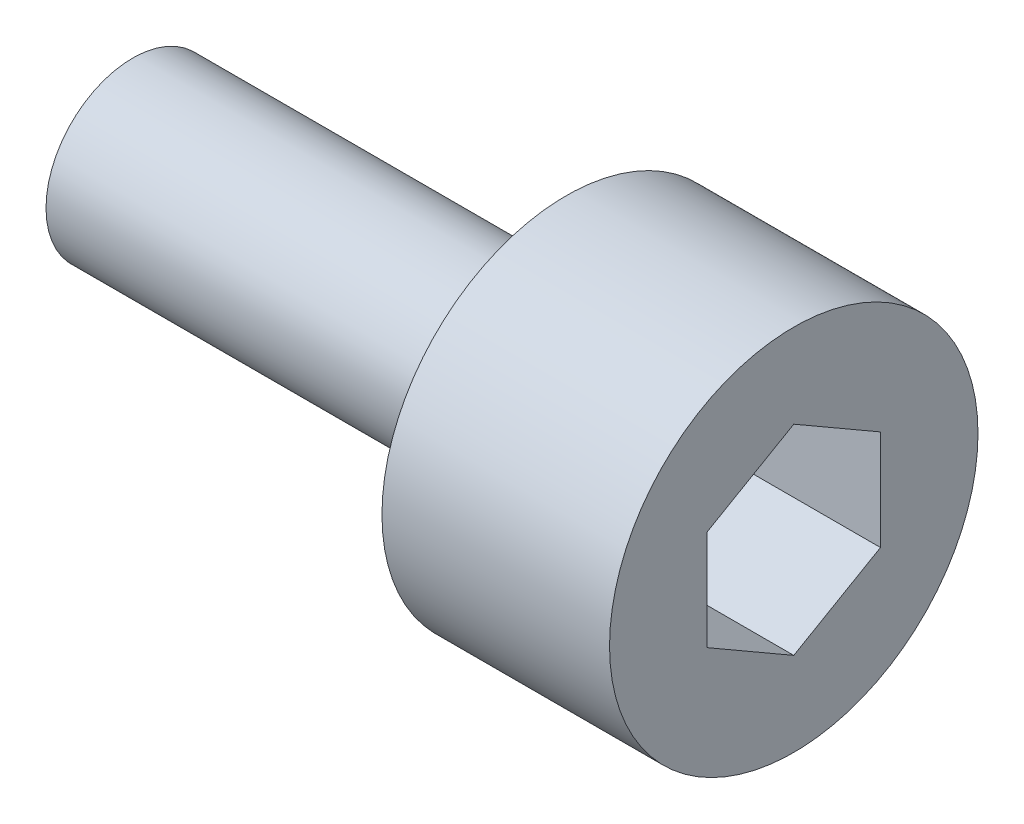
SolidWorks part; units mm, degrees
ref_plane "Front Plane" through (0, 0, 0) normal (0, 0, 1) x (1, 0, 0)
ref_plane "Top Plane" through (0, 0, 0) normal (0, 1, 0) x (1, 0, 0)
ref_plane "Right Plane" through (0, 0, 0) normal (1, 0, 0) x (0, 0, -1)
sketch "Sketch1" plane through (0, 0, 0) normal (1, 0, 0) x (0, 0, -1)
  circle A0 centre (0, 0) radius 4.25
  dimension "D1" = 8.5
extrude "Boss-Extrude1" add sketch "Sketch1" along normal blind 5.25
sketch "Sketch2" plane through (5.25, 0, 0) normal (1, 0, 0) x (0, 0, -1)
  line L1 (0, 2.3094) -> (-2, 1.1547)
  line L2 (-2, 1.1547) -> (-2, -1.1547)
  line L3 (-2, -1.1547) -> (0, -2.3094)
  line L4 (0, -2.3094) -> (2, -1.1547)
  line L5 (2, -1.1547) -> (2, 1.1547)
  line L6 (2, 1.1547) -> (0, 2.3094)
  circle A0 centre (0, 0) radius 2 construction
  dimension "D1" = 4
extrude "Cut-Extrude1" cut sketch "Sketch2" against normal blind 3.6
sketch "Sketch3" plane through (0, 0, 0) normal (-1, 0, 0) x (0, 0, 1)
  circle A0 centre (0, 0) radius 2
  dimension "D1" = 4
extrude "Boss-Extrude2" add sketch "Sketch3" along normal blind 10
